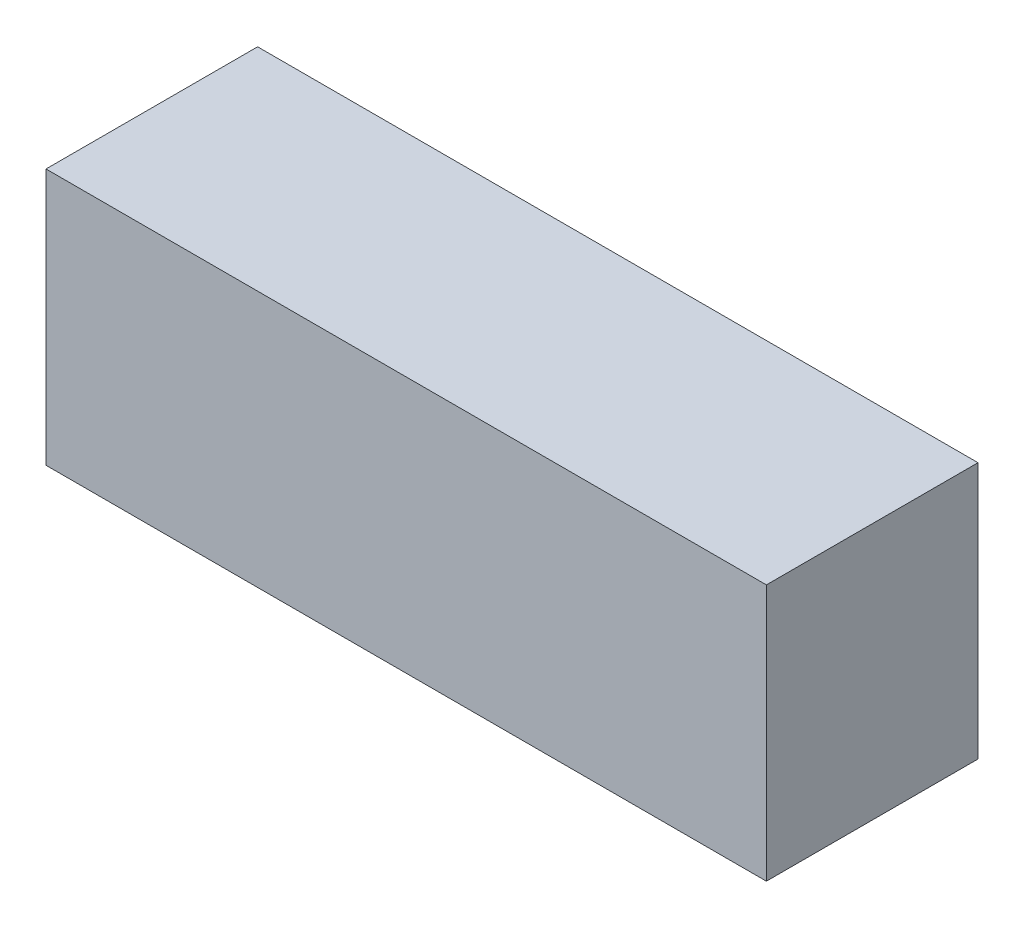
SolidWorks part; units mm, degrees
material "ABS"
ref_plane "Спереди" through (0, 0, 0) normal (0, 0, 1) x (1, 0, 0)
ref_plane "Сверху" through (0, 0, 0) normal (0, 1, 0) x (1, 0, 0)
ref_plane "Справа" through (0, 0, 0) normal (1, 0, 0) x (0, 0, -1)
sketch "Эскиз1" plane through (0, 0, 0) normal (0, 0, 1) x (1, 0, 0)
  line L1 (-80, -28.5) -> (80, -28.5)
  line L2 (-80, -28.5) -> (-80, 28.5)
  line L3 (-80, 28.5) -> (80, 28.5)
  line L4 (80, -28.5) -> (80, 28.5)
  line L5 (-80, -28.5) -> (80, 28.5) construction
  line L6 (-80, 28.5) -> (80, -28.5) construction
  point P0 (0, 0)
  dimension "D1" = 160
  dimension "D2" = 57
extrude "Бобышка-Вытянуть1" add sketch "Эскиз1" along normal blind 47
